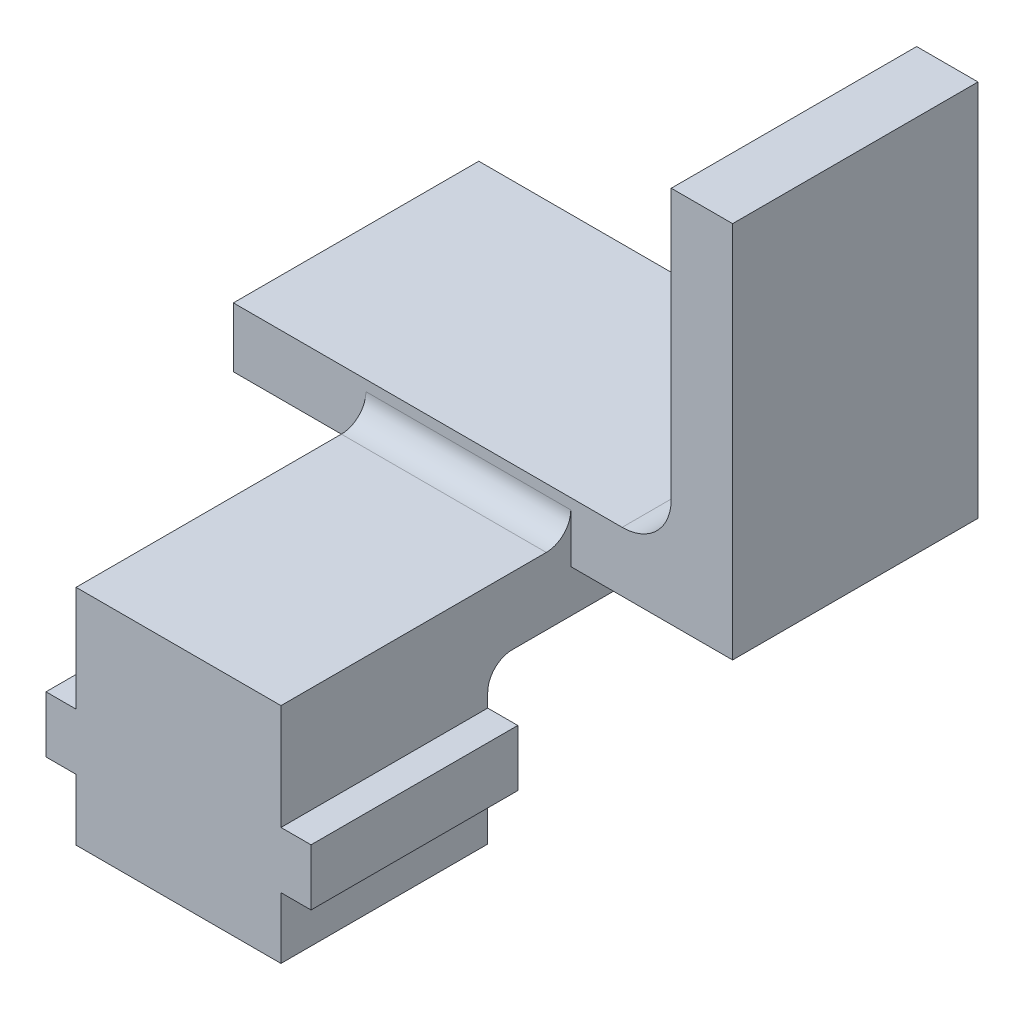
SolidWorks part; units mm, degrees
ref_plane "Front Plane" through (0, 0, 0) normal (0, 0, 1) x (1, 0, 0)
ref_plane "Top Plane" through (0, 0, 0) normal (0, 1, 0) x (1, 0, 0)
ref_plane "Right Plane" through (0, 0, 0) normal (1, 0, 0) x (0, 0, -1)
sketch "Sketch1" plane through (0, 0, 0) normal (0, 0, 1) x (1, 0, 0)
  line L0 (0, 0) -> (0, -4.191)
  line L1 (0, -4.191) -> (-1.5558, -4.191)
  line L2 (-1.5558, -4.191) -> (-1.5558, -7.112)
  line L3 (-1.5558, -7.112) -> (0, -7.112)
  line L4 (0, -7.112) -> (0, -10.287)
  line L5 (0, -10.287) -> (10.6045, -10.287)
  line L6 (10.6045, -10.287) -> (10.6045, -7.112)
  line L7 (10.6045, -7.112) -> (12.1603, -7.112)
  line L8 (12.1603, -7.112) -> (12.1603, -4.191)
  line L9 (12.1603, -4.191) -> (10.6045, -4.191)
  line L10 (10.6045, -4.191) -> (10.6045, 0)
  line L11 (10.6045, 0) -> (18.9772, 0)
  line L12 (18.9772, 0) -> (18.9772, 19.558)
  line L13 (18.9772, 19.558) -> (15.8022, 19.558)
  line L14 (15.8022, 19.558) -> (15.8022, 3.089)
  line L15 (15.8022, 3.089) -> (-6.858, 3.089)
  line L16 (-6.858, 3.089) -> (-6.858, 0)
  line L17 (-6.858, 0) -> (0, 0)
  line L18 (5.3022, -10.287) -> (5.3022, 13.589) construction
  circle A0 centre (5.3022, 13.589) radius 10.5 construction
  dimension "D9" = 21
  dimension "D1" = 10.6045
  dimension "D2" = 2.921
  dimension "D3" = 3.175
  dimension "D4" = 4.191
  dimension "D5" = 13.716
  dimension "D6" = 3.175
  dimension "D7" = 19.558
  dimension "D8" = 23.876
  dimension "D10" = 6.858
extrude "Boss-Extrude1" add sketch "Sketch1" along normal blind 12.7
fillet "Fillet1" radius 2.54 1 edges at (15.8022, 3.089, 6.35)
sketch "Sketch2" plane through (0, 0, 12.7) normal (0, 0, 1) x (1, 0, 0)
  line L0 (0, 0) -> (0, 1.27)
  line L1 (0, 1.27) -> (10.6045, 1.27)
  line L2 (10.6045, 1.27) -> (10.6045, 0)
  line L18 (-6.858, 0) -> (0, 0)
  line L19 (0, 0) -> (0, -4.191)
  line L20 (0, -4.191) -> (-1.5558, -4.191)
  line L21 (-1.5558, -4.191) -> (-1.5558, -7.112)
  line L22 (-1.5558, -7.112) -> (0, -7.112)
  line L23 (0, -7.112) -> (0, -10.287)
  line L24 (0, -10.287) -> (10.6045, -10.287)
  line L25 (10.6045, -10.287) -> (10.6045, -7.112)
  line L26 (10.6045, -7.112) -> (12.1603, -7.112)
  line L27 (12.1603, -7.112) -> (12.1603, -4.191)
  line L28 (12.1603, -4.191) -> (10.6045, -4.191)
  line L29 (10.6045, -4.191) -> (10.6045, 0)
  line L30 (10.6045, 0) -> (18.9772, 0)
  line L31 (18.9772, 0) -> (18.9772, 19.558)
  line L32 (18.9772, 19.558) -> (15.8022, 19.558)
  line L33 (15.8022, 19.558) -> (15.8022, 5.629)
  line L34 (13.2622, 3.089) -> (-6.858, 3.089)
  line L35 (-6.858, 3.089) -> (-6.858, 0)
  line L37 (0, 0) -> (0, -4.191)
  line L38 (0, -4.191) -> (-1.5558, -4.191)
  line L39 (-1.5558, -4.191) -> (-1.5558, -7.112)
  line L40 (-1.5558, -7.112) -> (0, -7.112)
  line L41 (0, -7.112) -> (0, -10.287)
  line L42 (0, -10.287) -> (10.6045, -10.287)
  line L43 (10.6045, -10.287) -> (10.6045, -7.112)
  line L44 (10.6045, -7.112) -> (12.1603, -7.112)
  line L45 (12.1603, -7.112) -> (12.1603, -4.191)
  line L46 (12.1603, -4.191) -> (10.6045, -4.191)
  line L47 (10.6045, -4.191) -> (10.6045, 0)
  arc A1 (13.2622, 3.089) -> (15.8022, 5.629) centre (13.2622, 5.629) ccw
  dimension "D2" = 1.27
  dimension "D1" = 0
extrude "Boss-Extrude2" add sketch "Sketch2" along normal blind 15
sketch "Sketch3" plane through (0, 0, 0) normal (0, 0, -1) x (-1, 0, 0)
  line L0 (-13.2622, 3.089) -> (6.858, 3.089) construction
  line L1 (-13.4086, -2.211) -> (7.0294, -2.211)
  line L2 (-13.4086, -2.211) -> (-13.4086, -13.6193)
  line L3 (-13.4086, -13.6193) -> (7.0294, -13.6193)
  line L4 (7.0294, -2.211) -> (7.0294, -13.6193)
  dimension "D1" = 5.3
extrude "Cut-Extrude1" cut sketch "Sketch3" against normal blind 17
fillet "Fillet2" radius 1.27 2 edges at (5.3022, 1.27, 12.7) (5.3022, -2.211, 17)
